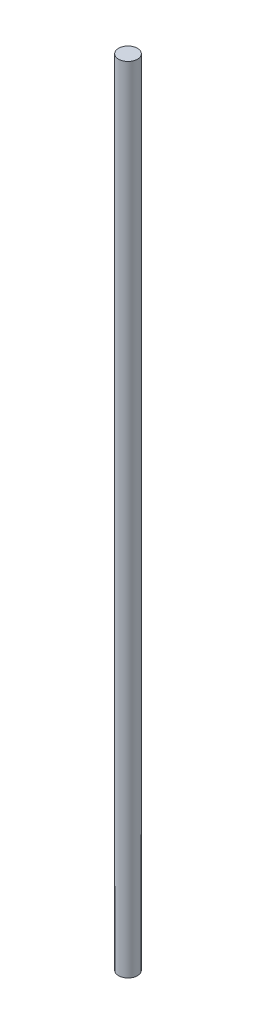
SolidWorks part; units mm, degrees
ref_plane "Front Plane" through (0, 0, 0) normal (0, 0, 1) x (1, 0, 0)
ref_plane "Top Plane" through (0, 0, 0) normal (0, 1, 0) x (1, 0, 0)
ref_plane "Right Plane" through (0, 0, 0) normal (1, 0, 0) x (0, 0, -1)
sketch "Sketch1" plane through (0, 0, 0) normal (0, 1, 0) x (1, 0, 0)
  circle A0 centre (0, 0) radius 4.7625
  dimension "D1" = 9.525
extrude "Boss-Extrude1" add sketch "Sketch1" along normal blind 400
